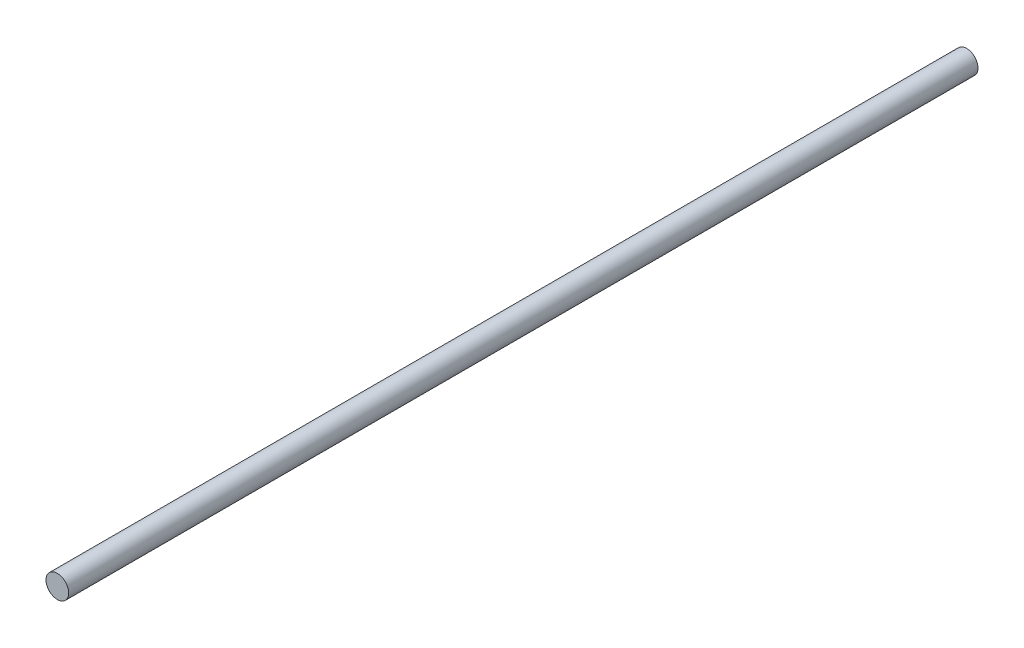
SolidWorks part; units mm, degrees
ref_plane "Front Plane" through (0, 0, 0) normal (0, 0, 1) x (1, 0, 0)
ref_plane "Top Plane" through (0, 0, 0) normal (0, 1, 0) x (1, 0, 0)
ref_plane "Right Plane" through (0, 0, 0) normal (1, 0, 0) x (0, 0, -1)
sketch "Sketch1" plane through (0, 0, 0) normal (0, 0, 1) x (1, 0, 0)
  circle A0 centre (0, 0) radius 10
  dimension "D1" = 20
extrude "Boss-Extrude1" add sketch "Sketch1" along normal blind 800
